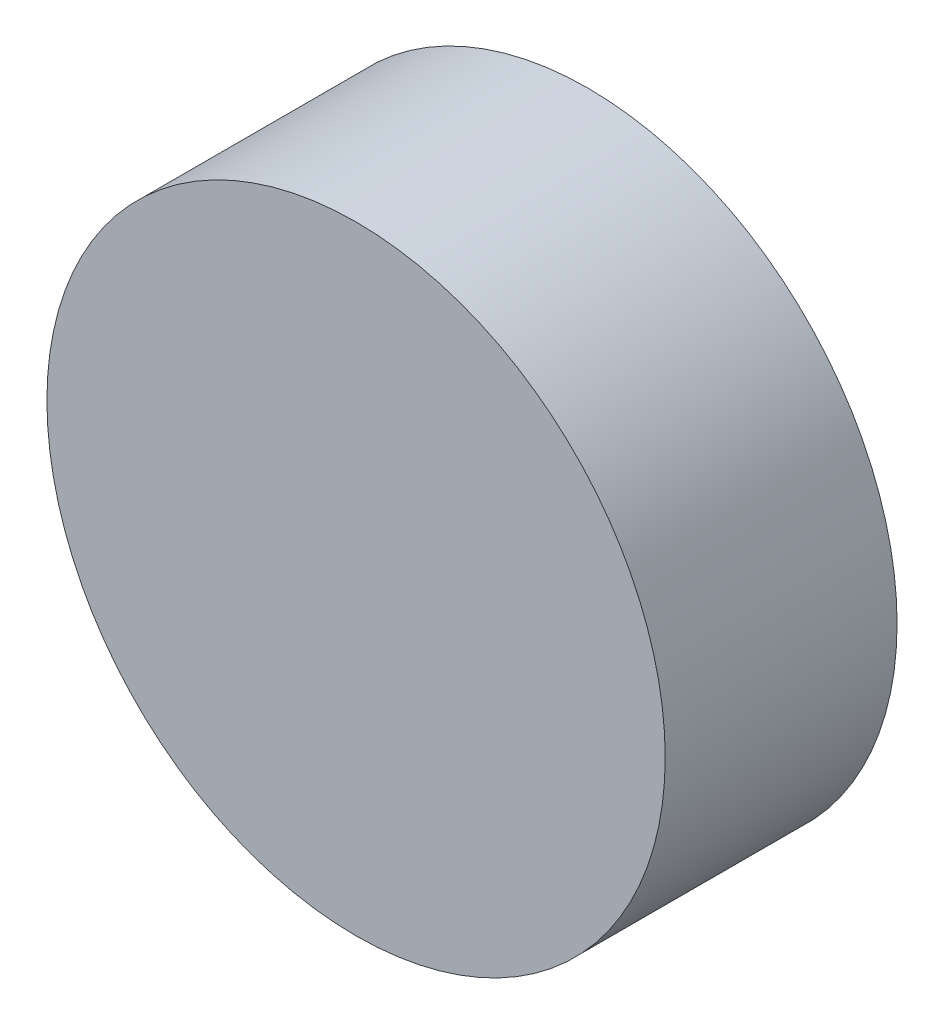
SolidWorks part; units mm, degrees
ref_plane "Front Plane" through (0, 0, 0) normal (0, 0, 1) x (1, 0, 0)
ref_plane "Top Plane" through (0, 0, 0) normal (0, 1, 0) x (1, 0, 0)
ref_plane "Right Plane" through (0, 0, 0) normal (1, 0, 0) x (0, 0, -1)
sketch "Sketch1" plane through (0, 0, 0) normal (0, 0, 1) x (1, 0, 0)
  circle A0 centre (0, 0) radius 4
  dimension "D1" = 8
extrude "Boss-Extrude1" add sketch "Sketch1" along normal blind 3
